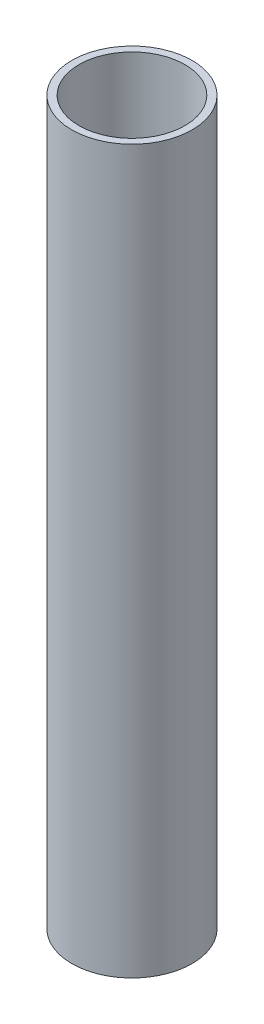
SolidWorks part; units mm, degrees
ref_plane "Front Plane" through (0, 0, 0) normal (0, 0, 1) x (1, 0, 0)
ref_plane "Top Plane" through (0, 0, 0) normal (0, 1, 0) x (1, 0, 0)
ref_plane "Right Plane" through (0, 0, 0) normal (1, 0, 0) x (0, 0, -1)
sketch "Sketch1" plane through (0, 0, 0) normal (0, 1, 0) x (1, 0, 0)
  circle A0 centre (0, 0) radius 12.7
  circle A1 centre (0, 0) radius 11.176
  dimension "D1" = 25.4
  dimension "D2" = 22.352
extrude "Boss-Extrude1" add sketch "Sketch1" along normal blind 152.4
